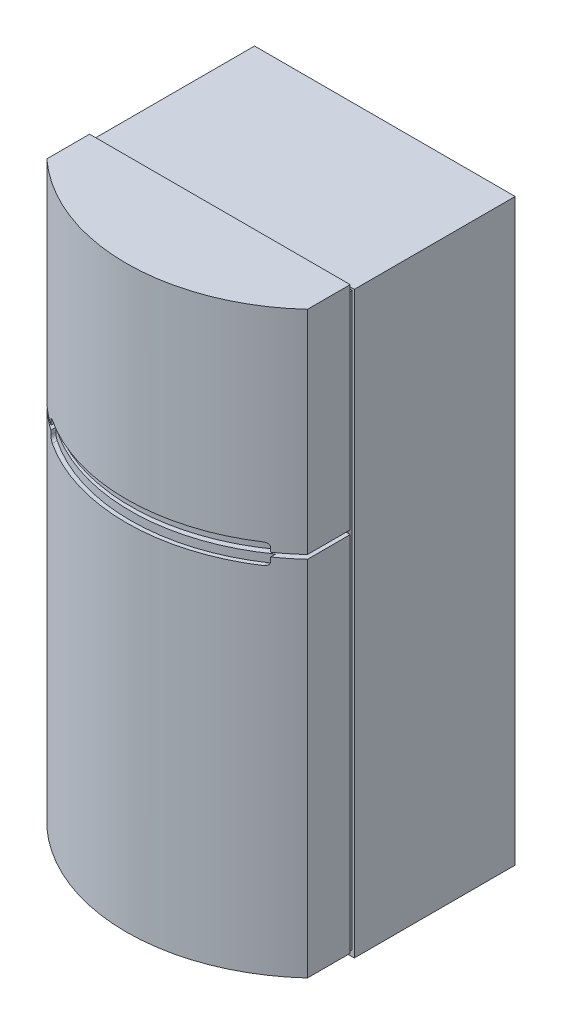
SolidWorks part; units mm, degrees
ref_plane "Front Plane" through (0, 0, 0) normal (0, 0, 1) x (1, 0, 0)
ref_plane "Top Plane" through (0, 0, 0) normal (0, 1, 0) x (1, 0, 0)
ref_plane "Right Plane" through (0, 0, 0) normal (1, 0, 0) x (0, 0, -1)
sketch "Sketch1" plane through (0, 0, 0) normal (0, 1, 0) x (1, 0, 0)
  line L1 (-405, -250) -> (405, -250)
  line L2 (-405, -250) -> (-405, 250)
  line L3 (-405, 250) -> (405, 250)
  line L4 (405, -250) -> (405, 250)
  line L5 (-405, -250) -> (405, 250) construction
  line L6 (-405, 250) -> (405, -250) construction
  point P0 (0, 0)
  dimension "D1" = 500
  dimension "D2" = 810
extrude "Boss-Extrude1" add sketch "Sketch1" along normal blind 1800
sketch "Sketch2" plane through (0, 0, 0) normal (0, 1, 0) x (1, 0, 0)
  line L0 (405, -250) -> (405, 250) construction
  line L1 (-405, -262.7) -> (405, -262.7)
  line L2 (-405, -262.7) -> (-405, -395.5833)
  line L3 (-405, -395.5833) -> (405, -395.5833) construction
  line L4 (405, -262.7) -> (405, -395.5833)
  line L5 (-405, 250) -> (-405, -250) construction
  line L6 (-405, -250) -> (405, -250) construction
  line L7 (0, -553.402) -> (0, -250) construction
  line L8 (405, 250) -> (-405, 250) construction
  arc A0 (-405, -395.5833) -> (405, -395.5833) centre (0, 45.17) ccw
  dimension "D1" = 12.7
  dimension "D2" = 803.402
extrude "Boss-Extrude2" add sketch "Sketch2" along normal blind 1800 from offset 19.05 separate body
ref_plane "Plane1" through (0, 0, 553.402) normal (0, 0, 1) x (1, 0, 0)
sketch "Sketch3" plane through (0, 0, 553.402) normal (0, 0, 1) x (1, 0, 0)
  line L0 (-405, 1819.05) -> (-405, 19.05) construction
  line L1 (-405, 1158.8433) -> (405, 1158.8433)
  line L2 (-405, 1158.8433) -> (-405, 1146.1433)
  line L3 (-405, 1146.1433) -> (405, 1146.1433)
  line L4 (405, 1158.8433) -> (405, 1146.1433)
  line L5 (405, 1819.05) -> (405, 19.05) construction
  dimension "D1" = 12.7
extrude "Cut-Extrude1" cut sketch "Sketch3" against normal blind 1712.976
sketch "Sketch4" plane through (0, 0, 553.402) normal (0, 0, 1) x (1, 0, 0)
  line L0 (405, 1819.05) -> (405, 1158.8433) construction
  line L1 (-328.8, 1184.2433) -> (328.8, 1184.2433)
  line L2 (-341.5, 1171.5433) -> (-341.5, 1133.4433)
  line L3 (-328.8, 1120.7433) -> (328.8, 1120.7433)
  line L4 (341.5, 1171.5433) -> (341.5, 1133.4433)
  line L5 (0, 1184.2433) -> (0, 1158.8433) construction
  line L6 (-405, 1158.8433) -> (405, 1158.8433) construction
  line L7 (0, 1146.1433) -> (0, 1120.7433) construction
  line L8 (405, 1146.1433) -> (-405, 1146.1433) construction
  arc A0 (328.8, 1120.7433) -> (341.5, 1133.4433) centre (328.8, 1133.4433) ccw
  arc A1 (328.8, 1184.2433) -> (341.5, 1171.5433) centre (328.8, 1171.5433) cw
  arc A2 (-341.5, 1133.4433) -> (-328.8, 1120.7433) centre (-328.8, 1133.4433) ccw
  arc A3 (-328.8, 1184.2433) -> (-341.5, 1171.5433) centre (-328.8, 1171.5433) ccw
  point P16 (341.5, 1120.7433)
  point P19 (341.5, 1184.2433)
  dimension "D3" = 12.7
  dimension "D1" = 63.5
  dimension "D2" = 63.5
extrude "Cut-Extrude2" cut sketch "Sketch4" against normal offset from surface (113.6632 mm away) 12.7
sketch "Sketch5" plane through (0, 0, 250) normal (0, 0, 1) x (1, 0, 0)
  line L0 (-405, 0) -> (405, 0) construction
  line L1 (405, 1146.1433) -> (405, 19.05) construction
  line L2 (-405, 1146.1433) -> (-405, 19.05) construction
  line L5 (-405, 1800) -> (405, 1800) construction
  line L12 (-398.65, 19.05) -> (398.65, 19.05)
  line L13 (398.65, 19.05) -> (398.65, 1793.65)
  line L14 (398.65, 1793.65) -> (-398.65, 1793.65)
  line L15 (-398.65, 1793.65) -> (-398.65, 19.05)
  dimension "D1" = 19.05
  dimension "D2" = 6.35
  dimension "D3" = 6.35
  dimension "D4" = 6.35
extrude "Extrude-Thin1" add sketch "Sketch5" along normal blind 12.7 separate body thin thin type one direction reverse wall 12.7
sketch "Sketch6" plane through (0, 0, 250) normal (0, 0, 1) x (1, 0, 0)
  line L0 (-302.626, 0) -> (-268.0274, 13.4836)
  line L1 (-405, 0) -> (405, 0) construction
  line L2 (-268.0274, 13.4836) -> (268.0274, 13.4836)
  line L3 (0, 13.4836) -> (0, 0) construction
  line L4 (302.626, 0) -> (-302.626, 0)
  line L5 (302.626, 0) -> (268.0274, 13.4836)
extrude "Cut-Extrude3" cut sketch "Sketch6" against normal through all
